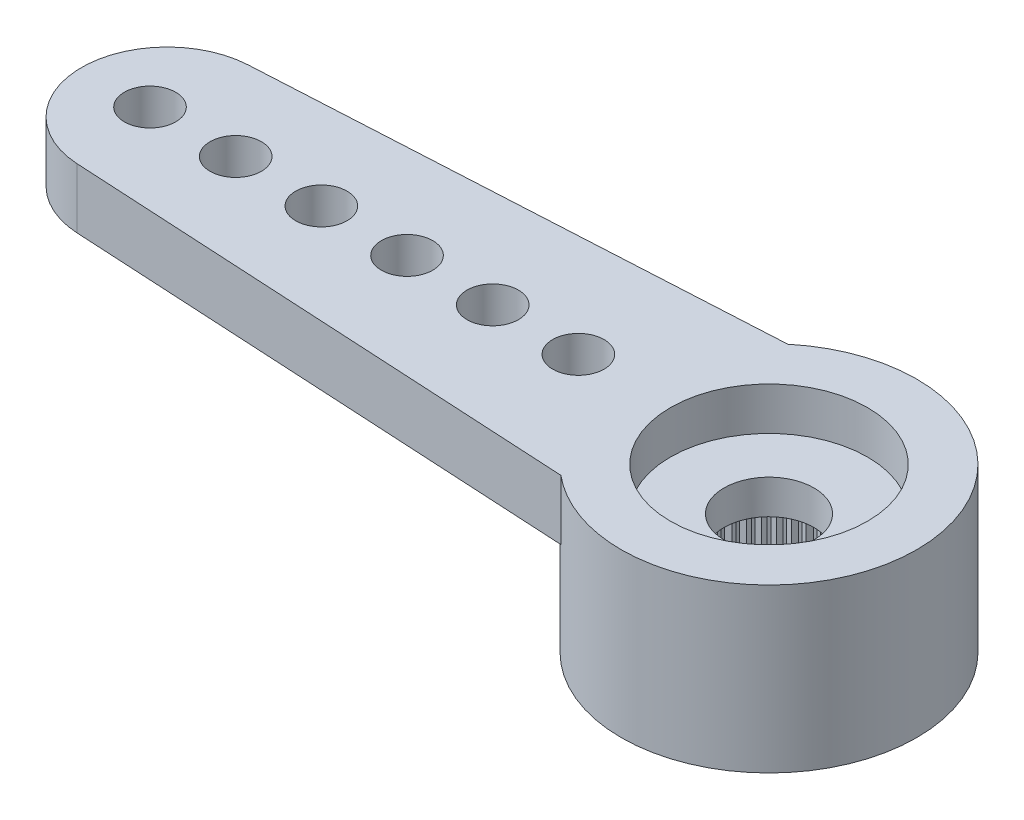
SolidWorks part; units mm, degrees
material "PVC Rígido"
ref_plane "Plano frontal" through (0, 0, 0) normal (0, 0, 1) x (1, 0, 0)
ref_plane "Plano superior" through (0, 0, 0) normal (0, 1, 0) x (1, 0, 0)
ref_plane "Plano direito" through (0, 0, 0) normal (1, 0, 0) x (0, 0, -1)
sketch "Esboço1" plane through (0, 0, 0) normal (0, 1, 0) x (1, 0, 0)
  line L0 (0, 0) -> (-14.05, 0) construction
  line L1 (-14.1591, 1.997) -> (-2.2091, 2.65)
  line L2 (-2.2091, -2.65) -> (-14.1591, -1.997)
  arc A0 (-2.2091, -2.65) -> (-2.2091, 2.65) centre (0, 0) ccw
  arc A1 (-14.1591, 1.997) -> (-14.1591, -1.997) centre (-14.05, 0) ccw
  dimension "D1" = 6.9
  dimension "D2" = 4
  dimension "D3" = 19.5
  dimension "D4" = 5.3
extrude "Ressalto-extrusão1" add sketch "Esboço1" against normal blind 1.4
sketch "Esboço2" plane through (0, -1.4, 0) normal (0, -1, 0) x (1, 0, 0)
  arc A0 (-2.2091, -2.65) -> (-2.2091, 2.65) centre (0, 0) ccw construction
  circle A1 centre (0, 0) radius 3.45
extrude "Ressalto-extrusão2" add sketch "Esboço2" along normal offset from surface (2.4 mm away) 3.8 up to face at (-7.242, 0, 0)
hole_wizard "Furo4" positions "Esboço9" profile "Esboço10" legacy end condition through all
sketch "Esboço9" plane through (0, 0, 0) normal (0, 1, 0) x (1, 0, 0)
  line L1 (-14.45, 0) -> (0, 0) construction
  arc A2 (-14.1591, 1.997) -> (-14.1591, -1.997) centre (-14.05, 0) ccw construction
  point P0 (-14.45, 0)
  point P19 (-16.05, 0)
  dimension "D1" = 1.6
sketch "Esboço10" plane through (-14.45, 0, 0) normal (1, 0, 0) x (0, 0, 1)
  line L0 (0, 0) -> (0, 3.8)
  line L1 (0, 3.8) -> (0.6, 3.8)
  line L2 (0.6, 3.8) -> (0.6, 0)
  line L3 (0.6, 0) -> (0, 0)
  line L4 (0, 110) -> (0, -10) construction
  dimension "Diameter" = 1.2
  dimension "Depth" = 3.8
pattern_linear "Padrão linear1" count 6 spacing 2 along (1, 0, 0) of "Furo4"
hole_wizard "Furo1" positions "Esboço3" profile "Esboço4" legacy
sketch "Esboço3" plane through (0, -3.8, 0) normal (0, -1, 0) x (-1, 0, 0)
  point P0 (0, 0)
sketch "Esboço4" plane through (0, -3.8, 0) normal (1, 0, 0) x (0, 0, -1)
  line L0 (0, 0) -> (0, 2)
  line L1 (0, 2) -> (2.475, 2)
  line L2 (2.475, 2) -> (2.475, 0)
  line L3 (2.475, 0) -> (0, 0)
  line L4 (0, 110) -> (0, -10) construction
  dimension "Diameter" = 4.95
  dimension "Depth" = 2
hole_wizard "Furo2" positions "Esboço5" profile "Esboço6" legacy
sketch "Esboço5" plane through (0, 0, 0) normal (0, 1, 0) x (1, 0, 0)
  point P0 (0, 0)
sketch "Esboço6" plane through (0, 0, 0) normal (1, 0, 0) x (0, 0, 1)
  line L0 (0, 0) -> (0, 1)
  line L1 (0, 1) -> (2.3, 1)
  line L2 (2.3, 1) -> (2.3, 0)
  line L3 (2.3, 0) -> (0, 0)
  line L4 (0, 110) -> (0, -10) construction
  dimension "Diameter" = 4.6
  dimension "Depth" = 1
hole_wizard "Furo3" positions "Esboço7" profile "Esboço8" legacy end condition through all
sketch "Esboço7" plane through (0, 0, 0) normal (0, 1, 0) x (1, 0, 0)
  point P0 (0, 0)
sketch "Esboço8" plane through (0, 0, 0) normal (1, 0, 0) x (0, 0, 1)
  line L0 (0, 0) -> (0, 3.8)
  line L1 (0, 3.8) -> (1.05, 3.8)
  line L2 (1.05, 3.8) -> (1.05, 0)
  line L3 (1.05, 0) -> (0, 0)
  line L4 (0, 110) -> (0, -10) construction
  dimension "Diameter" = 2.1
  dimension "Depth" = 3.8
sketch "Esboço11" plane through (0, -3.8, 0) normal (0, -1, 0) x (1, 0, 0)
  line L0 (-0.0981, 2.4731) -> (0, 2.375)
  line L1 (0, 2.375) -> (0.0981, 2.4731)
  line L2 (0, 0) -> (0, 2.475) construction
  circle A0 centre (0, 0) radius 2.375 construction
  circle A1 centre (0, 0) radius 2.475
  arc A2 (0.0981, 2.4731) -> (-0.0981, 2.4731) centre (0, 0) ccw
  dimension "D3" = 4.75
  dimension "D2" = 0.1
  dimension "D1" = 0
extrude "Ressalto-extrusão3" add sketch "Esboço11" against normal up to surface (2 mm away) up to face at (0, -1.8, 1.05)
pattern_circular "PadrãoCircular1" count 60 over 360 about axis through (0, 0, 0) along (0, 1, 0) of "Ressalto-extrusão3"
ref_plane "Plane1" through (0, 10, 0) normal (0, 1, 0) x (1, 0, 0)
